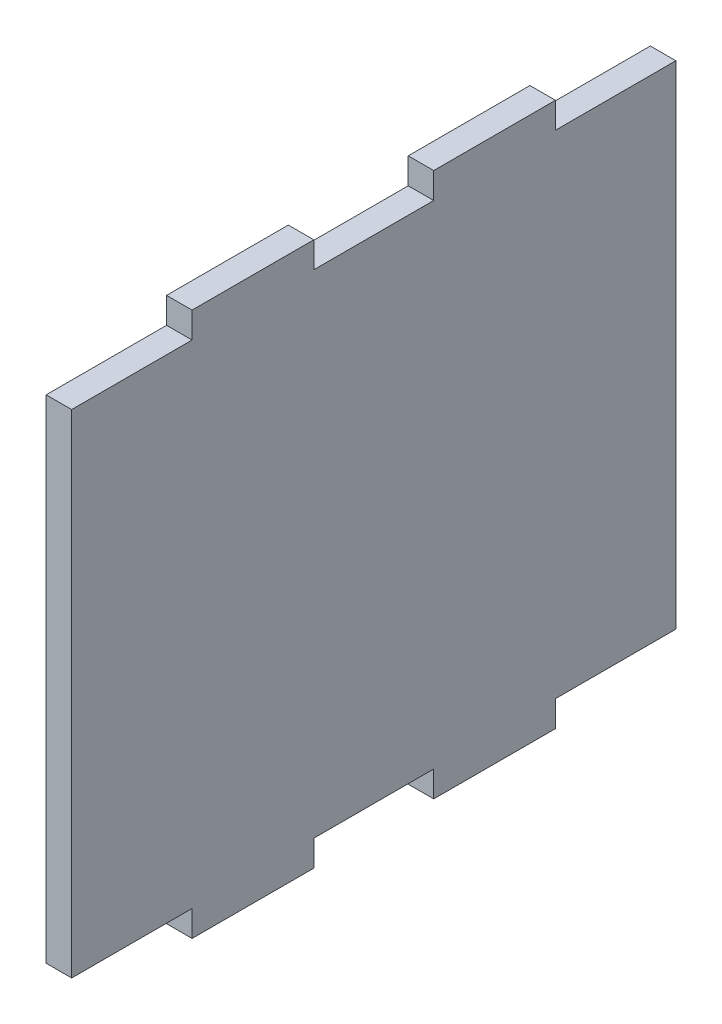
SolidWorks part; units mm, degrees
ref_plane "Front Plane" through (0, 0, 0) normal (0, 0, 1) x (1, 0, 0)
ref_plane "Top Plane" through (0, 0, 0) normal (0, 1, 0) x (1, 0, 0)
ref_plane "Right Plane" through (0, 0, 0) normal (1, 0, 0) x (0, 0, -1)
sketch "Sketch1" plane through (0, 0, 0) normal (1, 0, 0) x (0, 0, -1)
  line L1 (0, 0) -> (135, 0)
  line L2 (0, 0) -> (0, 122)
  line L3 (0, 122) -> (135, 122)
  line L4 (135, 0) -> (135, 122)
sketch "Sketch2" plane through (0, 0, 0) normal (1, 0, 0) x (0, 0, -1)
  line L0 (0, 116) -> (26.9, 116)
  line L1 (0, -8) -> (0, 6)
  line L2 (26.9, 116) -> (26.9, 121.8)
  line L3 (-162, 61) -> (162, 61) construction
  line L4 (26.9, 121.8) -> (54.1, 121.8)
  line L5 (54.1, 121.8) -> (54.1, 116)
  line L6 (54.1, 116) -> (80.9, 116)
  line L7 (80.9, 116) -> (80.9, 121.8)
  line L8 (80.9, 121.8) -> (108.1, 121.8)
  line L9 (108.1, 121.8) -> (108.1, 116)
  line L10 (108.1, 116) -> (135, 116)
  line L11 (135, -8) -> (0, -8)
  line L12 (135, 116) -> (135, 130)
  line L13 (135, 130) -> (0, 130)
  line L14 (0, 130) -> (0, 116)
  line L15 (135, 6) -> (135, -8)
  line L16 (108.1, 6) -> (135, 6)
  line L17 (108.1, 0.2) -> (108.1, 6)
  line L18 (80.9, 0.2) -> (108.1, 0.2)
  line L19 (80.9, 6) -> (80.9, 0.2)
  line L20 (54.1, 6) -> (80.9, 6)
  line L21 (54.1, 0.2) -> (54.1, 6)
  line L22 (26.9, 0.2) -> (54.1, 0.2)
  line L23 (26.9, 6) -> (26.9, 0.2)
  line L24 (0, 6) -> (26.9, 6)
  point P7 (0, 61)
extrude "Boss-Extrude1" add sketch "Sketch1" along normal blind 5.7
extrude "Cut-Extrude1" cut sketch "Sketch2" along normal blind 57
